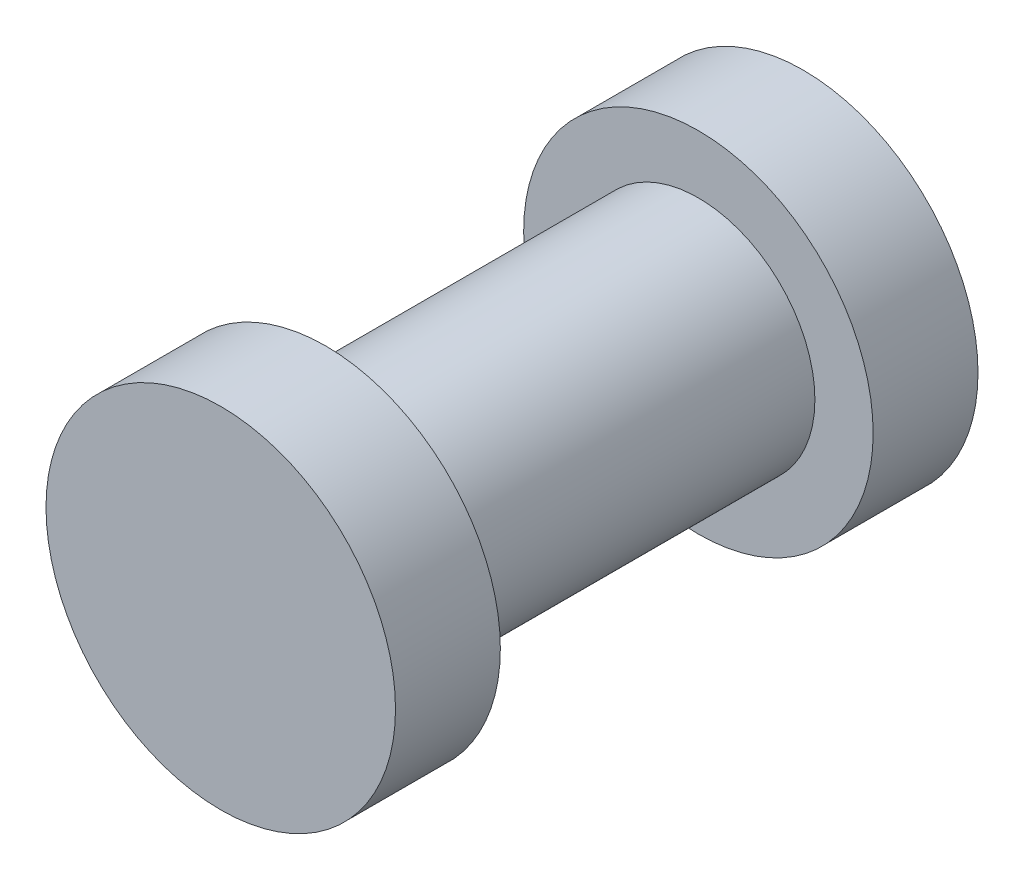
SolidWorks part; units mm, degrees
ref_plane "Front Plane" through (0, 0, 0) normal (0, 0, 1) x (1, 0, 0)
ref_plane "Top Plane" through (0, 0, 0) normal (0, 1, 0) x (1, 0, 0)
ref_plane "Right Plane" through (0, 0, 0) normal (1, 0, 0) x (0, 0, -1)
sketch "Sketch1" plane through (0, 0, 0) normal (0, 0, 1) x (1, 0, 0)
  circle A0 centre (0, 0) radius 2
  dimension "D1" = 4
extrude "Boss-Extrude1" add sketch "Sketch1" along normal mid plane 10
sketch "Sketch2" plane through (0, 0, 5) normal (0, 0, 1) x (1, 0, 0)
  circle A0 centre (0, 0) radius 3
  dimension "D1" = 6
extrude "Boss-Extrude2" add sketch "Sketch2" against normal blind 1.8
mirror "Mirror1" about plane through (0, 0, 0) normal (0, 0, 1) of "Boss-Extrude2"
